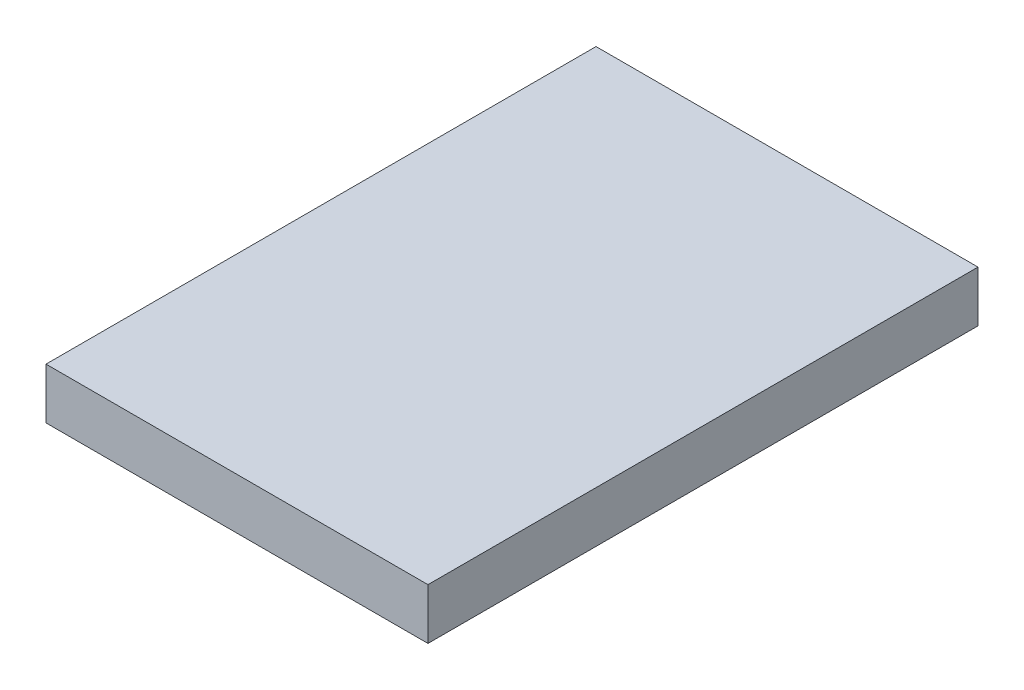
SolidWorks part; units mm, degrees
material "Silicon"
ref_plane "Front Plane" through (0, 0, 0) normal (0, 0, 1) x (1, 0, 0)
ref_plane "Top Plane" through (0, 0, 0) normal (0, 1, 0) x (1, 0, 0)
ref_plane "Right Plane" through (0, 0, 0) normal (1, 0, 0) x (0, 0, -1)
sketch "Sketch1" plane through (0, 0, 0) normal (0, 1, 0) x (1, 0, 0)
  line L1 (-3.75, 5.4) -> (3.75, 5.4)
  line L2 (-3.75, 5.4) -> (-3.75, -5.4)
  line L3 (-3.75, -5.4) -> (3.75, -5.4)
  line L4 (3.75, 5.4) -> (3.75, -5.4)
  line L5 (-3.75, 5.4) -> (3.75, -5.4) construction
  line L6 (-3.75, -5.4) -> (3.75, 5.4) construction
  point P0 (0, 0)
  dimension "D1" = 7.5
  dimension "D2" = 10.8
extrude "Boss-Extrude1" add sketch "Sketch1" along normal blind 1
